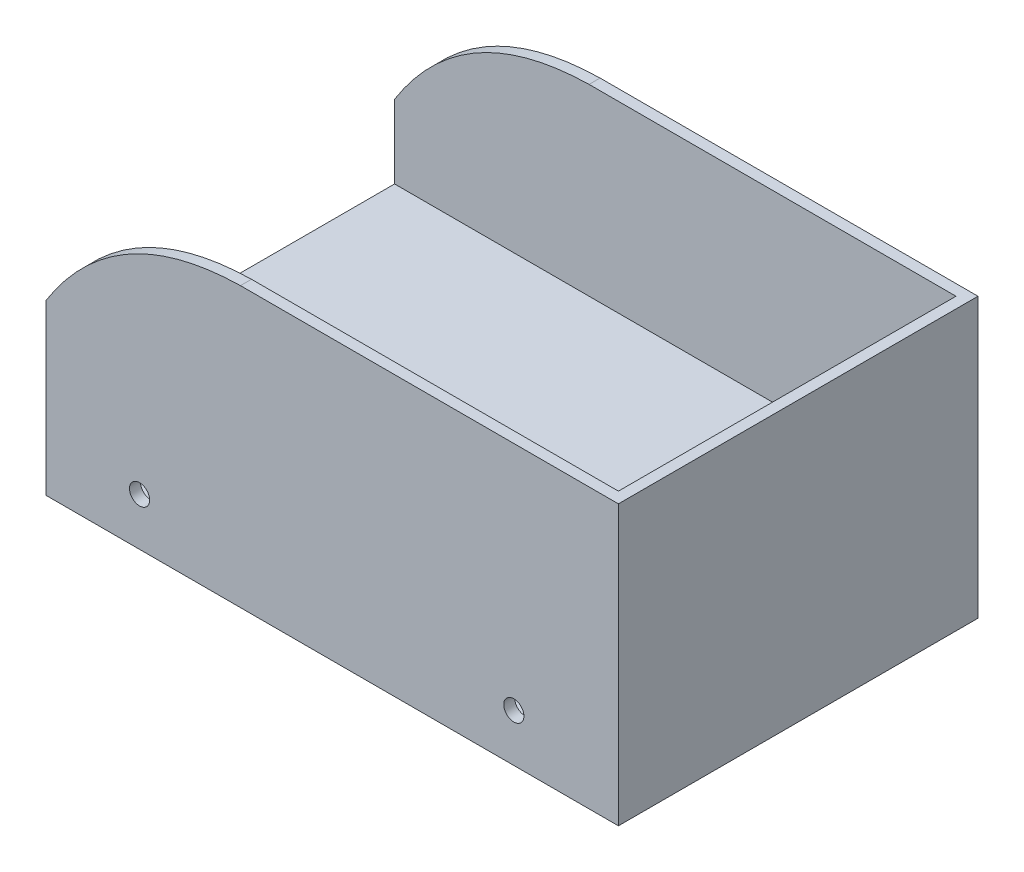
SolidWorks part; units mm, degrees
ref_plane "Front Plane" through (0, 0, 0) normal (0, 0, 1) x (1, 0, 0)
ref_plane "Top Plane" through (0, 0, 0) normal (0, 1, 0) x (1, 0, 0)
ref_plane "Right Plane" through (0, 0, 0) normal (1, 0, 0) x (0, 0, -1)
sketch "Sketch1" plane through (0, 0, 0) normal (0, 0, 1) x (1, 0, 0)
  line L4 (-765, 0) -> (765, 0)
  line L5 (765, 0) -> (765, 500)
  line L6 (765, 500) -> (-235, 500)
  line L7 (-765, 0) -> (-765, 200)
  line L8 (-765, 0) -> (-765, -230)
  line L9 (-765, -230) -> (765, -230)
  line L10 (765, -230) -> (765, 0)
  spline S0 degree 2 poles (-235, 500) (-580.9437, 493.3248) (-765, 200) knots 0 0 0 1 1 1
  point P3 (0, 0)
  dimension "D5" = 422.2
  dimension "D1" = 1000
  dimension "D2" = 500
  dimension "D3" = 1530
  dimension "D4" = 200
  dimension "D6" = 225.48
  dimension "D7" = 230
extrude "Boss-Extrude3" add sketch "Sketch1" along normal blind 30 contours L6 S0 L7 L4 L5 | L9 L10 L4 L8
sketch "Sketch9" plane through (0, 0, 30) normal (0, 0, 1) x (1, 0, 0)
  line L0 (-765, -230) -> (765, -230) construction
  line L1 (765, -230) -> (765, 500) construction
  line L2 (-765, -230) -> (-765, 200) construction
  circle A0 centre (-510, -130) radius 27.5
  circle A2 centre (510, -130) radius 27.5
  dimension "D1" = 55
  dimension "D3" = 55
  dimension "D4" = 100
  dimension "D6" = 100
  dimension "D8" = 255
  dimension "D9" = 255
extrude "Cut-Extrude1" cut sketch "Sketch9" against normal through all
sketch "Sketch10" plane through (0, -230, 0) normal (0, -1, 0) x (1, 0, 0)
  line L1 (-765, 30) -> (765, 30)
  line L2 (-765, 30) -> (-765, -950)
  line L3 (-765, -950) -> (765, -950)
  line L4 (765, 30) -> (765, -950)
  dimension "D1" = 980
  dimension "D2" = 1530
extrude "Boss-Extrude4" add sketch "Sketch10" along normal blind 30
ref_plane "Plane3" through (0, 0, -460) normal (0, 0, 1) x (1, 0, 0)
sketch "Sketch11" plane through (765, 0, 0) normal (1, 0, 0) x (0, 0, -1)
  line L1 (-30, -260) -> (950, -260)
  line L2 (-30, -260) -> (-30, 500)
  line L3 (-30, 500) -> (950, 500)
  line L4 (950, -260) -> (950, 500)
  dimension "D1" = 760
  dimension "D2" = 980
extrude "Boss-Extrude5" add sketch "Sketch11" along normal blind 30
mirror "Mirror3" about plane through (0, 0, -460) normal (0, 0, 1) of "Cut-Extrude1", "Boss-Extrude3", "Boss-Extrude5"
sketch "Sketch12" plane through (765, 0, 0) normal (-1, 0, 0) x (0, 0, 1)
  line L0 (0, -230) -> (0, 500) construction
  line L1 (0, -30) -> (-920, -30)
  line L2 (0, -30) -> (0, 0)
  line L3 (0, 0) -> (-920, 0)
  line L4 (-920, -30) -> (-920, 0)
  line L5 (-920, -230) -> (0, -230) construction
  dimension "D1" = 920
  dimension "D2" = 200
  dimension "D3" = 30
extrude "Boss-Extrude6" add sketch "Sketch12" along normal blind 1530
sketch "Sketch13" plane through (-765, 0, 0) normal (-1, 0, 0) x (0, 0, 1)
  line L6 (-920, -30) -> (0, -30) construction
  line L7 (-680, -30) -> (-660, -30)
  line L8 (-680, -30) -> (-680, -230)
  line L9 (-680, -230) -> (-660, -230)
  line L10 (-660, -30) -> (-660, -230)
  line L11 (0, -230) -> (-920, -230) construction
  line L12 (-920, -30) -> (0, -30) construction
  line L13 (-260, -30) -> (-240, -30)
  line L14 (-260, -30) -> (-260, -230)
  line L15 (-260, -230) -> (-240, -230)
  line L16 (-240, -30) -> (-240, -230)
  line L21 (-460, -16.5) -> (-460, 16.5) construction
  dimension "D1" = 20
  dimension "D2" = 20
  dimension "D3" = 400
  dimension "D4" = 200
extrude "Boss-Extrude7" add sketch "Sketch13" against normal blind 1530
sketch "Sketch14" plane through (0, 0, -240) normal (0, 0, 1) x (1, 0, 0)
  line L0 (-765, -230) -> (-765, -30) construction
  line L1 (765, -230) -> (-765, -230) construction
  line L2 (765, -230) -> (765, -30) construction
  circle A0 centre (-510, -130) radius 27.5
  circle A1 centre (0, -130) radius 40
  circle A2 centre (510, -130) radius 27.5
  dimension "D1" = 55
  dimension "D2" = 80
  dimension "D3" = 55
  dimension "D4" = 255
  dimension "D5" = 100
  dimension "D6" = 100
  dimension "D7" = 255
  dimension "D8" = 100
  dimension "D9" = 765
extrude "Cut-Extrude3" cut sketch "Sketch14" against normal blind 500
sketch "Sketch17" plane through (765, 0, 0) normal (-1, 0, 0) x (0, 0, 1)
  line L0 (-660, -230) -> (-260, -230) construction
  line L1 (-515, -205.06) -> (-405, -205.06)
  line L2 (-515, -205.06) -> (-515, -230)
  line L3 (-515, -230) -> (-405, -230)
  line L4 (-405, -205.06) -> (-405, -230)
  line L5 (-460, -16.5) -> (-460, 16.5) construction
  point P8 (-460, -205.06)
  dimension "D1" = 0
  dimension "D2" = 24.94
  dimension "D3" = 110
  dimension "D4" = 0
extrude "Boss-Extrude8" add sketch "Sketch17" along normal blind 300 from offset 500
